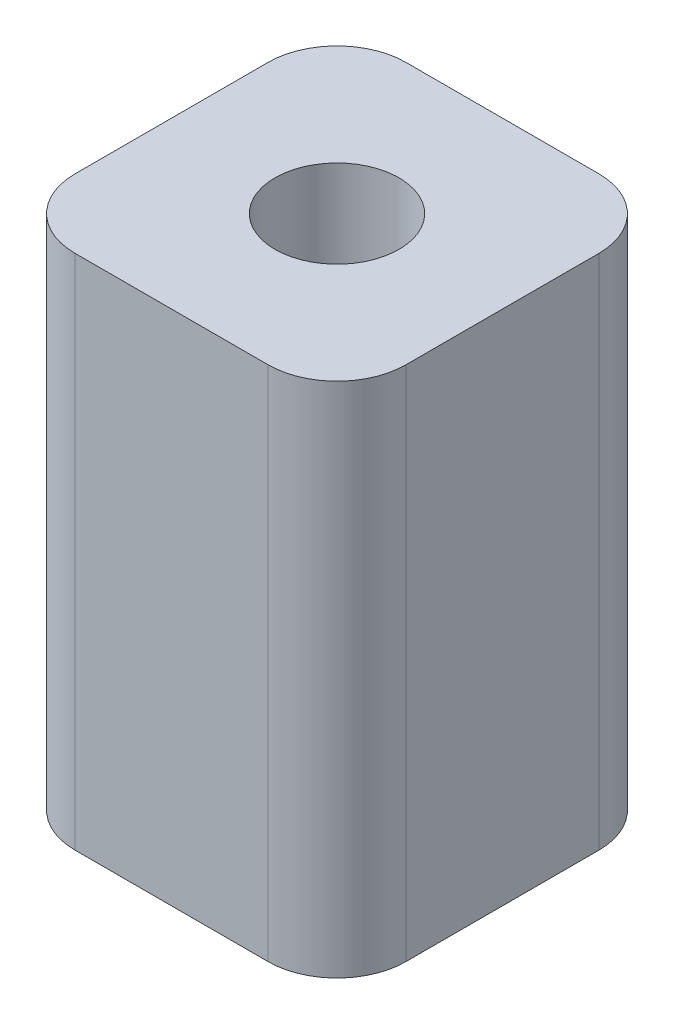
SolidWorks part; units mm, degrees
ref_plane "Plano frontal" through (0, 0, 0) normal (0, 0, 1) x (1, 0, 0)
ref_plane "Plano superior" through (0, 0, 0) normal (0, 1, 0) x (1, 0, 0)
ref_plane "Plano direito" through (0, 0, 0) normal (1, 0, 0) x (0, 0, -1)
sketch "Sketch1" plane through (0, 0, 0) normal (0, 1, 0) x (1, 0, 0)
  line L1 (-4.8, 4.8) -> (4.8, 4.8)
  line L2 (-4.8, 4.8) -> (-4.8, -4.8)
  line L3 (-4.8, -4.8) -> (4.8, -4.8)
  line L4 (4.8, 4.8) -> (4.8, -4.8)
  circle A0 centre (0, 0) radius 1.5 construction
  circle A1 centre (0, 0) radius 1.8
  point P9 (0, 0)
  point P10 (0, 4.8)
  point P11 (-4.8, 0)
  dimension "D1" = 3
  dimension "D3" = 3
  dimension "D4" = 3
  dimension "D2" = 0.3
extrude "Boss-Extrude1" add sketch "Sketch1" along normal mid plane 15
fillet "Fillet1" radius 2 4 edges at (4.8, 0, -4.8) (4.8, 0, 4.8) (-4.8, 0, -4.8) (-4.8, 0, 4.8)
